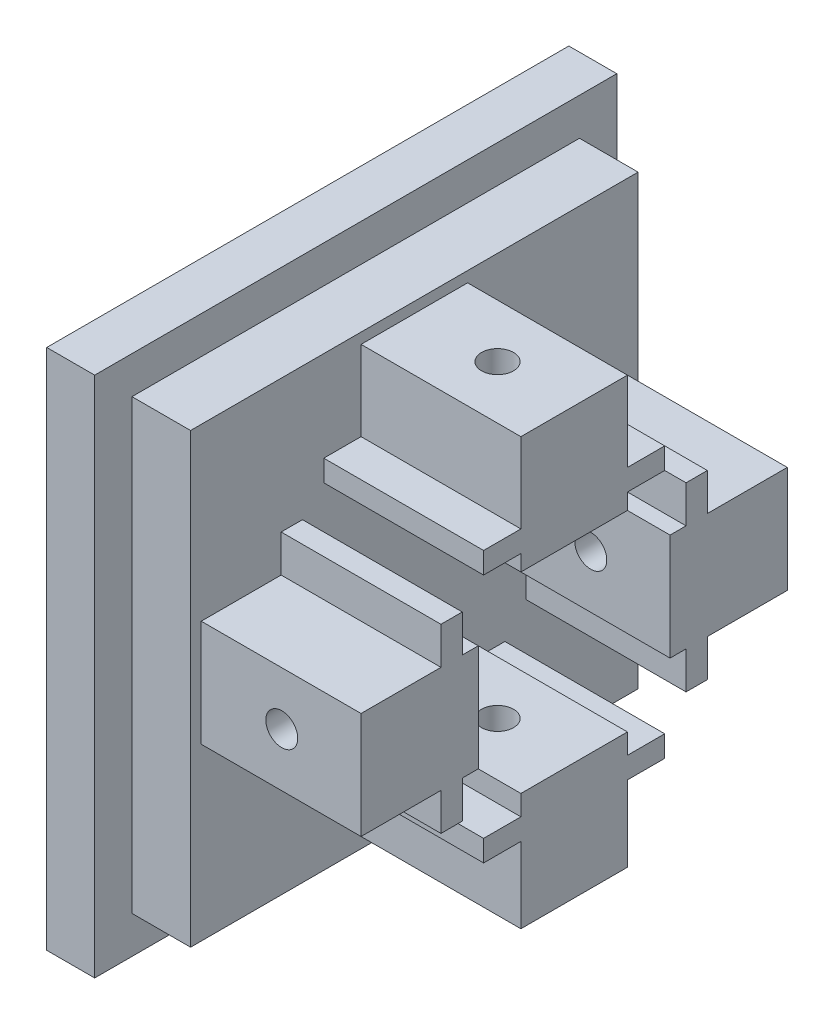
SolidWorks part; units mm, degrees
ref_plane "Front Plane" through (0, 0, 0) normal (0, 0, 1) x (1, 0, 0)
ref_plane "Top Plane" through (0, 0, 0) normal (0, 1, 0) x (1, 0, 0)
ref_plane "Right Plane" through (0, 0, 0) normal (1, 0, 0) x (0, 0, -1)
sketch "Sketch1" plane through (0, 0, 0) normal (1, 0, 0) x (0, 0, -1)
  line L1 (24.5, 24.5) -> (-24.5, 24.5)
  line L2 (24.5, 24.5) -> (24.5, -24.5)
  line L3 (24.5, -24.5) -> (-24.5, -24.5)
  line L4 (-24.5, 24.5) -> (-24.5, -24.5)
  line L5 (24.5, 24.5) -> (-24.5, -24.5) construction
  line L6 (24.5, -24.5) -> (-24.5, 24.5) construction
  point P0 (0, 0)
  dimension "D1" = 49
  dimension "D2" = 49
extrude "Boss-Extrude1" add sketch "Sketch1" along normal blind 4.5
sketch "Sketch3" plane through (4.5, 0, 0) normal (1, 0, 0) x (0, 0, -1)
  line L0 (24.5, 24.5) -> (-24.5, 24.5) construction
  line L1 (-21, 21) -> (21, 21)
  line L2 (-21, 21) -> (-21, -21)
  line L3 (-21, -21) -> (21, -21)
  line L4 (21, 21) -> (21, -21)
  line L5 (-21, 21) -> (21, -21) construction
  line L6 (-21, -21) -> (21, 21) construction
  line L7 (-24.5, 24.5) -> (-24.5, -24.5) construction
  point P0 (0, 0)
  dimension "D1" = 3.5
  dimension "D2" = 3.5
extrude "Boss-Extrude3" add sketch "Sketch3" along normal blind 5.5
sketch "Sketch4" plane through (10, 0, 0) normal (1, 0, 0) x (0, 0, -1)
  line L1 (20, 20) -> (-20, 20)
  line L2 (20, 20) -> (20, -20)
  line L3 (20, -20) -> (-20, -20)
  line L4 (-20, 20) -> (-20, -20)
  line L5 (0, -20) -> (0, 20) construction
  line L6 (20, 0) -> (-20, 0) construction
  line L7 (-20, -5) -> (-9, -5)
  line L8 (-20, -5) -> (-20, 5)
  line L9 (-20, 5) -> (-9, 5)
  line L10 (-9, -5) -> (-9, 5)
  line L11 (-14.5, 5) -> (-14.5, -5) construction
  line L12 (-20, 0) -> (-9, 0) construction
  line L13 (5, -9) -> (-5, -9)
  line L14 (5, -9) -> (5, -20)
  line L15 (5, -20) -> (-5, -20)
  line L16 (-5, -9) -> (-5, -20)
  line L17 (0, -20) -> (0, -9) construction
  line L18 (5, -14.5) -> (-5, -14.5) construction
  line L19 (-5, 20) -> (5, 20)
  line L20 (-5, 20) -> (-5, 9)
  line L21 (-5, 9) -> (5, 9)
  line L22 (5, 20) -> (5, 9)
  line L23 (0, 9) -> (0, 20) construction
  line L24 (-5, 14.5) -> (5, 14.5) construction
  line L25 (9, -5) -> (20, -5)
  line L26 (9, -5) -> (9, 5)
  line L27 (9, 5) -> (20, 5)
  line L28 (20, -5) -> (20, 5)
  line L29 (14.5, 5) -> (14.5, -5) construction
  line L30 (9, 0) -> (20, 0) construction
  point P0 (0, 0)
  point P4 (-14.5, 0)
  point P8 (0, -14.5)
  point P12 (0, 14.5)
  point P16 (14.5, 0)
  dimension "D1" = 40
  dimension "D2" = 40
  dimension "D3" = 10
  dimension "D4" = 0
  dimension "D5" = 11
  dimension "D6" = 10
  dimension "D7" = 11
  dimension "D8" = 0
  dimension "D9" = 11
  dimension "D10" = 10
  dimension "D11" = 0
  dimension "D12" = 10
  dimension "D13" = 11
  dimension "D14" = 0
extrude "Boss-Extrude5" add sketch "Sketch4" along normal blind 15 contours L27 L26 L25 L2 | L13 L16 L3 L14 | L7 L10 L9 L4 | L22 L1 L20 L21
hole_wizard "Ø3.0mm Dowel Slot1" positions "Sketch11" profile "Sketch12" size "Ø3.0" standard "ANSI Metric" slot yes end condition through all
sketch "Sketch11" plane through (0, 0, -20) normal (0, 0, -1) x (-1, 0, 0)
  point P0 (-17.559, 0)
sketch "Sketch12" plane through (17.559, 0, -20) normal (1, 0, 0) x (0, 1, 0)
  line L0 (0, 0) -> (0, 44.5)
  line L1 (0, 44.5) -> (1.5, 44.5)
  line L2 (1.5, 44.5) -> (1.5, 0)
  line L5 (1.5, 0) -> (0, 0)
  line L11 (0, -6.35) -> (0, 107.95) construction
  dimension "Thru Hole Dia." = 3
  dimension "Thru Hole Depth" = 44.5
hole_wizard "Ø3.0mm Dowel Slot2" positions "Sketch13" profile "Sketch14" size "Ø3.0" standard "ANSI Metric" slot yes end condition through all
sketch "Sketch13" plane through (0, 20, 0) normal (0, 1, 0) x (1, 0, 0)
  point P0 (17.8091, 0)
sketch "Sketch14" plane through (17.8091, 20, 0) normal (1, 0, 0) x (0, 0, 1)
  line L0 (0, 0) -> (0, 44.5)
  line L1 (0, 44.5) -> (1.5, 44.5)
  line L2 (1.5, 44.5) -> (1.5, 0)
  line L5 (1.5, 0) -> (0, 0)
  line L11 (0, -6.35) -> (0, 107.95) construction
  dimension "Thru Hole Dia." = 3
  dimension "Thru Hole Depth" = 44.5
sketch "Sketch15" plane through (0, 0, 5) normal (0, 0, 1) x (1, 0, 0)
  line L0 (25, -9) -> (25, -20) construction
  line L1 (10, -12.9) -> (25, -12.9)
  line L2 (10, -12.9) -> (10, -10.9)
  line L3 (10, -10.9) -> (25, -10.9)
  line L4 (25, -12.9) -> (25, -10.9)
  line L5 (17.5, -10.9) -> (17.5, -12.9) construction
  line L6 (10, -11.9) -> (25, -11.9) construction
  line L7 (25, -20) -> (10, -20) construction
  point P0 (17.5, -11.9)
  dimension "D1" = 2
  dimension "D2" = 15
  dimension "D3" = 0
  dimension "D4" = 7.1
extrude "Boss-Extrude7" add sketch "Sketch15" along normal blind 3.5 and the other way blind 13.5
hole_wizard "Ø3.0mm Dowel Slot3" positions "3DSketch1" profile "Sketch17" size "Ø3.0" standard "ANSI Metric" slot yes end condition through all
sketch3d "3DSketch1"
  line L0 (17.8091, -20, 0) -> (17.8091, -12.9, 0) construction
  point P0 (17.8091, -20, 0)
sketch "Sketch17" plane through (17.8091, -20, 0) normal (1, 0, 0) x (0, 0, -1)
  line L0 (0, 0) -> (0, 44.5)
  line L1 (0, 44.5) -> (1.5, 44.5)
  line L2 (1.5, 44.5) -> (1.5, 0)
  line L5 (1.5, 0) -> (0, 0)
  line L11 (0, -6.35) -> (0, 107.95) construction
  dimension "Thru Hole Dia." = 3
  dimension "Thru Hole Depth" = 44.5
sketch "Sketch18" plane through (0, 0, -5) normal (0, 0, -1) x (-1, 0, 0)
  line L0 (-25, 20) -> (-25, 9) construction
  line L1 (-10, 10.5) -> (-25, 10.5)
  line L2 (-10, 10.5) -> (-10, 12.5)
  line L3 (-10, 12.5) -> (-25, 12.5)
  line L4 (-25, 10.5) -> (-25, 12.5)
  line L5 (-17.5, 12.5) -> (-17.5, 10.5) construction
  line L6 (-10, 11.5) -> (-25, 11.5) construction
  line L7 (-25, 20) -> (-10, 20) construction
  point P0 (-17.5, 11.5)
  dimension "D1" = 2
  dimension "D2" = 15
  dimension "D3" = 0
  dimension "D4" = 7.5
extrude "Boss-Extrude8" add sketch "Sketch18" along normal blind 3.5 and the other way blind 13.5
hole_wizard "Ø3.0mm Dowel Slot5" positions "Sketch21" profile "Sketch22" size "Ø3.0" standard "ANSI Metric" slot yes end condition through all
sketch "Sketch21" plane through (0, 20, 0) normal (0, 1, 0) x (1, 0, 0)
  point P0 (17.8091, 0)
sketch "Sketch22" plane through (17.8091, 20, 0) normal (1, 0, 0) x (0, 0, 1)
  line L0 (0, 0) -> (0, 44.5)
  line L1 (0, 44.5) -> (1.5, 44.5)
  line L2 (1.5, 44.5) -> (1.5, 0)
  line L5 (1.5, 0) -> (0, 0)
  line L11 (0, -6.35) -> (0, 107.95) construction
  dimension "Thru Hole Dia." = 3
  dimension "Thru Hole Depth" = 44.5
sketch "Sketch23" plane through (0, -5, 0) normal (0, -1, 0) x (1, 0, 0)
  line L0 (25, -9) -> (25, -20) construction
  line L1 (10, -10.5) -> (25, -10.5)
  line L2 (10, -10.5) -> (10, -12.5)
  line L3 (10, -12.5) -> (25, -12.5)
  line L4 (25, -10.5) -> (25, -12.5)
  line L5 (17.5, -12.5) -> (17.5, -10.5) construction
  line L6 (10, -11.5) -> (25, -11.5) construction
  line L7 (25, -20) -> (10, -20) construction
  point P0 (17.5, -11.5)
  dimension "D1" = 15
  dimension "D2" = 2
  dimension "D3" = 0
  dimension "D4" = 7.5
extrude "Boss-Extrude9" add sketch "Sketch23" along normal blind 3.5 and the other way blind 13.5
sketch "Sketch24" plane through (0, -5, 0) normal (0, -1, 0) x (1, 0, 0)
  line L0 (25, 20) -> (25, 9) construction
  line L1 (10, 10.5) -> (25, 10.5)
  line L2 (10, 10.5) -> (10, 12.5)
  line L3 (10, 12.5) -> (25, 12.5)
  line L4 (25, 10.5) -> (25, 12.5)
  line L5 (17.5, 12.5) -> (17.5, 10.5) construction
  line L6 (10, 11.5) -> (25, 11.5) construction
  line L9 (25, 20) -> (10, 20) construction
  point P0 (17.5, 11.5)
  point P6 (25, 14.5)
  dimension "D1" = 2
  dimension "D2" = 15
  dimension "D3" = 0
  dimension "D4" = 7.5
extrude "Boss-Extrude10" add sketch "Sketch24" along normal blind 3.5 and the other way blind 13.5
hole_wizard "Ø3.0mm Dowel Slot6" positions "Sketch25" profile "Sketch26" size "Ø3.0" standard "ANSI Metric" slot yes end condition through all
sketch "Sketch25" plane through (0, 0, 20) normal (0, 0, 1) x (1, 0, 0)
  point P0 (17.559, 0)
sketch "Sketch26" plane through (17.559, 0, 20) normal (1, 0, 0) x (0, -1, 0)
  line L0 (0, 0) -> (0, 44.5)
  line L1 (0, 44.5) -> (1.5, 44.5)
  line L2 (1.5, 44.5) -> (1.5, 0)
  line L5 (1.5, 0) -> (0, 0)
  line L11 (0, -6.35) -> (0, 107.95) construction
  dimension "Thru Hole Dia." = 3
  dimension "Thru Hole Depth" = 44.5
